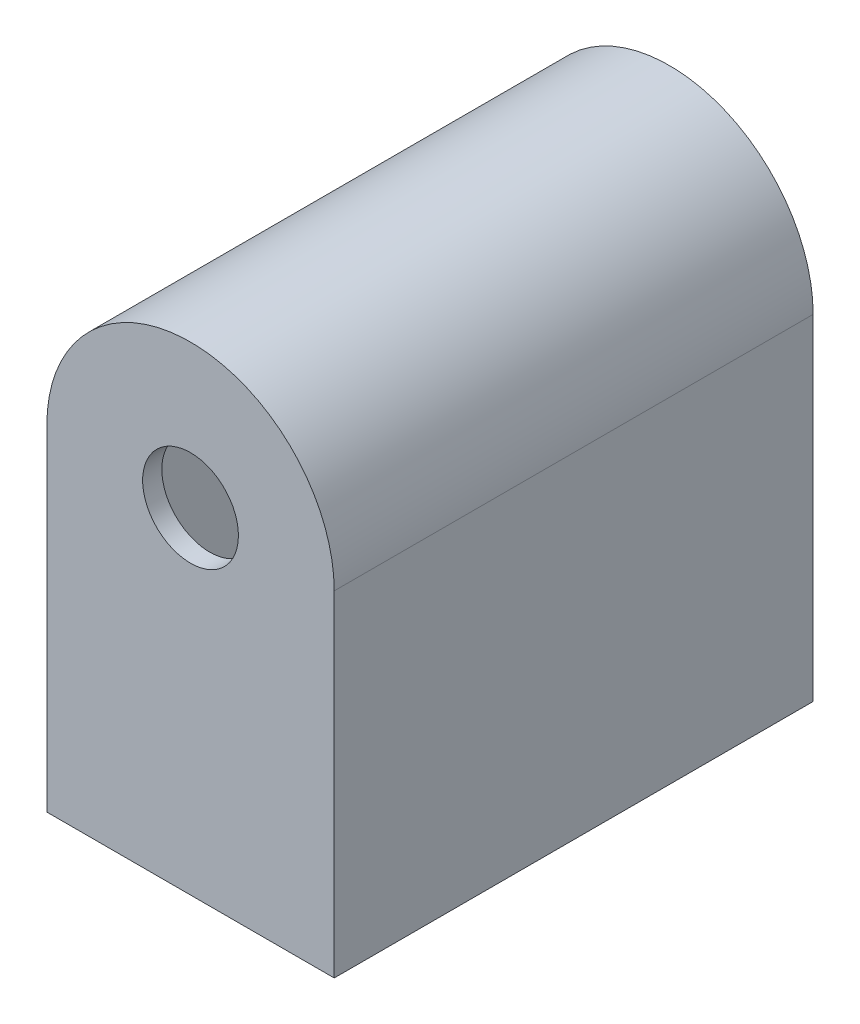
SolidWorks part; units mm, degrees
ref_plane "Plan de face" through (0, 0, 0) normal (0, 0, 1) x (1, 0, 0)
ref_plane "Plan de dessus" through (0, 0, 0) normal (0, 1, 0) x (1, 0, 0)
ref_plane "Plan de droite" through (0, 0, 0) normal (1, 0, 0) x (0, 0, -1)
sketch "Esquisse1" plane through (0, 0, 0) normal (0, 0, 1) x (1, 0, 0)
  line L1 (-15, -17.5) -> (15, -17.5)
  line L2 (-15, -17.5) -> (-15, 17.5)
  line L4 (15, -17.5) -> (15, 17.5)
  line L5 (-15, -17.5) -> (15, 17.5) construction
  line L6 (-15, 17.5) -> (15, -17.5) construction
  arc A0 (15, 17.5) -> (-15, 17.5) centre (0, 17.5) ccw
  circle A1 centre (0, 17.5) radius 5
  point P0 (0, 0)
  point P6 (0, 0)
  point P7 (-14.9701, 17.4649)
  point P10 (-1.0831, 15.0945)
  point P11 (0, 0)
  dimension "D2" = 10
  dimension "D3" = 50
  dimension "D1" = 30
extrude "Boss.-Extru.1" add sketch "Esquisse1" against normal blind 50
sketch "Esquisse2" plane through (0, 0, -50) normal (0, 0, -1) x (-1, 0, 0)
  line L6 (-13, 17.5) -> (-13, -15.5)
  line L7 (-13, -15.5) -> (13, -15.5)
  line L8 (13, -15.5) -> (13, 17.5)
  line L9 (-13, 17.5) -> (-13, -15.5)
  line L10 (-13, -15.5) -> (13, -15.5)
  line L11 (13, -15.5) -> (13, 17.5)
  arc A2 (13, 17.5) -> (-13, 17.5) centre (0, 17.5) ccw
  arc A3 (13, 17.5) -> (-13, 17.5) centre (0, 17.5) ccw
  dimension "D1" = 2
extrude "Enlèv. mat.-Extru.2" cut sketch "Esquisse2" against normal offset from surface (48 mm away) 2 up to face at (5, 17.5, 0)
